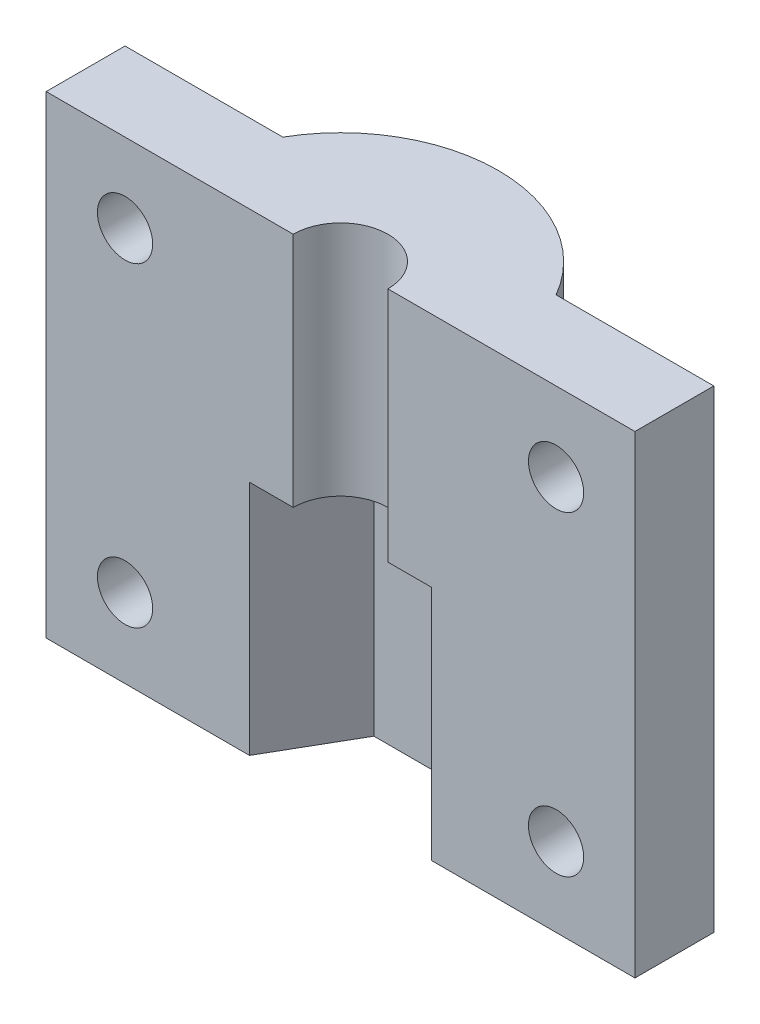
SolidWorks part; units mm, degrees
ref_plane "Спереди" through (0, 0, 0) normal (0, 0, 1) x (1, 0, 0)
ref_plane "Сверху" through (0, 0, 0) normal (0, 1, 0) x (1, 0, 0)
ref_plane "Справа" through (0, 0, 0) normal (1, 0, 0) x (0, 0, -1)
sketch "Эскиз1" plane through (0, 0, 0) normal (0, 1, 0) x (1, 0, 0)
  line L0 (-5.7735, 0) -> (-18.6603, 0)
  line L4 (5.7735, 0) -> (2.8868, 5)
  line L5 (2.8868, 5) -> (-2.8868, 5)
  line L6 (-2.8868, 5) -> (-5.7735, 0)
  line L7 (-18.6603, 0) -> (-18.6603, 5)
  line L8 (-18.6603, 5) -> (-8.6603, 5)
  line L9 (0, 0) -> (0, 15.3748) construction
  line L10 (5.7735, 0) -> (18.6603, 0)
  line L11 (18.6603, 0) -> (18.6603, 5)
  line L12 (18.6603, 5) -> (8.6603, 5)
  line L13 (-2.8868, -5) -> (0, -5) [skipped]
  line L14 (-5.7735, 0) -> (-4.3301, -2.5) [skipped]
  line L15 (4.3301, -2.5) -> (5.7735, 0) [skipped]
  circle A0 centre (0, 0) radius 5 construction
  arc A1 (8.6603, 5) -> (-8.6603, 5) centre (0, 0) ccw
  point P13 (7, 0)
  dimension "D2" = 20
  dimension "D3" = 10
  dimension "D4" = 5
extrude "Бобышка-Вытянуть1" add sketch "Эскиз1" along normal blind 15
sketch "Эскиз2" plane through (0, 15, 0) normal (0, 1, 0) x (1, 0, 0)
  line L0 (-18.6603, 5) -> (-8.6603, 5)
  line L1 (18.6603, 5) -> (18.6603, 0)
  line L2 (18.6603, 0) -> (10, 0)
  line L3 (-18.6603, 5) -> (-18.6603, 0)
  line L4 (-18.6603, 0) -> (-3, 0)
  line L5 (10, 0) -> (3, 0)
  line L6 (8.6603, 5) -> (18.6603, 5)
  arc A0 (3, 0) -> (-3, 0) centre (0, 0) ccw
  arc A1 (8.6603, 5) -> (-8.6603, 5) centre (0, 0) ccw
  dimension "D1" = 6
extrude "Бобышка-Вытянуть2" add sketch "Эскиз2" along normal blind 15
sketch "Эскиз3" plane through (0, 0, -5) normal (0, 0, -1) x (-1, 0, 0)
  line L0 (0, 0) -> (0, 34.4133) construction
  line L1 (2.8868, 0) -> (-2.8868, 0) construction
  line L2 (18.6603, 15) -> (-18.6603, 15) construction
  line L3 (18.6603, 30) -> (18.6603, 0) construction
  line L4 (-18.6603, 30) -> (-18.6603, 0) construction
  line L5 (-18.6603, 0) -> (-8.6603, 0) construction
  line L6 (-8.6603, 30) -> (-8.6603, 0) construction
  circle A0 centre (-13.6603, 5) radius 1.75
  circle A1 centre (-13.6603, 25) radius 1.75
  circle A2 centre (13.6603, 5) radius 1.75
  circle A3 centre (13.6603, 25) radius 1.75
  dimension "D1" = 3.5
  dimension "D2" = 5
  dimension "D3" = 5
extrude "Вырез-Вытянуть1" cut sketch "Эскиз3" against normal through all
